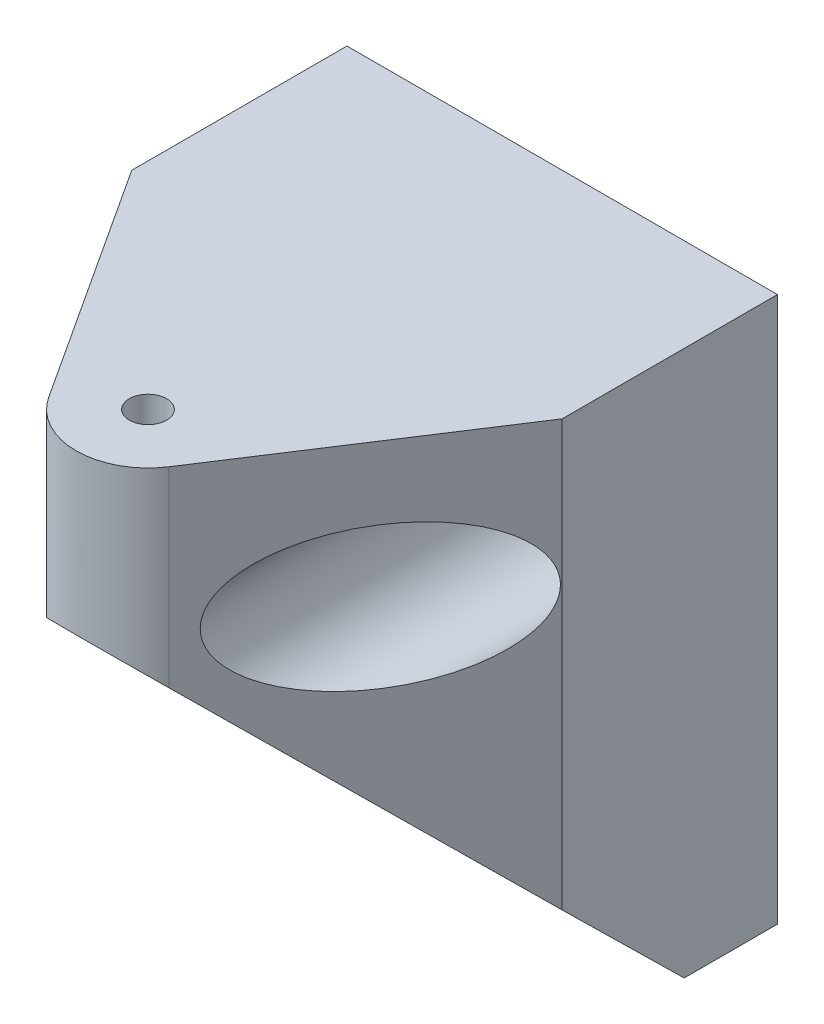
SolidWorks part; units mm, degrees
material "ABS"
ref_plane "Front Plane" through (0, 0, 0) normal (0, 0, 1) x (1, 0, 0)
ref_plane "Top Plane" through (0, 0, 0) normal (0, 1, 0) x (1, 0, 0)
ref_plane "Right Plane" through (0, 0, 0) normal (1, 0, 0) x (0, 0, -1)
sketch "Sketch2" plane through (0, 0, 0) normal (1, 0, 0) x (0, 0, -1)
  line L0 (0, 0) -> (-6.5, 0)
  line L1 (-35, 38) -> (-35, 28)
  line L2 (-35, 38) -> (0, 38)
  line L3 (0, 38) -> (0, 0)
  line L4 (-35, 28) -> (-6.5, 0)
  dimension "D1" = 38
  dimension "D2" = 6.5
  dimension "D3" = 35
  dimension "D4" = 10
extrude "Boss-Extrude1" add sketch "Sketch2" along normal blind 30
sketch "Sketch3" plane through (0, 0, 0) normal (0, 0, -1) x (-1, 0, 0)
  line L0 (-25, 28) -> (-30, 28) construction
  line L1 (-30, 0) -> (-30, 38) construction
  line L2 (-5, 28) -> (0, 28) construction
  line L3 (0, 0) -> (0, 38) construction
  line L4 (-30, 38) -> (0, 38) construction
  circle A0 centre (-25, 28) radius 2.6
  circle A1 centre (-5, 28) radius 2.6
  dimension "D1" = 5.2
  dimension "D3" = 20
  dimension "D4" = 10
extrude "Cut-Extrude1" cut sketch "Sketch3" against normal up to next
sketch "Sketch4" plane through (0, 0, 0) normal (0, 0, -1) x (-1, 0, 0)
  circle A0 centre (-25, 28) radius 4.95
  circle A1 centre (-5, 28) radius 4.95
  dimension "D1" = 9.9
extrude "Cut-Extrude2" cut sketch "Sketch4" against normal up to next from offset 6.5 offset against normal yes
sketch "Sketch5" plane through (0, 38, 0) normal (0, 1, 0) x (1, 0, 0)
  line L0 (30, 0) -> (0, 0) construction
  line L1 (15, -28.87) -> (15, 0) construction
  circle A0 centre (15, -28.87) radius 1.3
  dimension "D1" = 28.87
  dimension "D2" = 2.6
extrude "Cut-Extrude3" cut sketch "Sketch5" against normal up to next
sketch "Sketch6" plane through (0, 38, 0) normal (0, 1, 0) x (1, 0, 0)
  line L0 (0, -35) -> (30, -35)
  line L1 (30, -35) -> (30, -15)
  line L2 (30, 0) -> (30, -35) construction
  line L3 (30, -15) -> (19.1898, -31.5987)
  line L4 (10.8102, -31.5987) -> (0, -15)
  line L5 (0, 0) -> (0, -35) construction
  line L6 (0, -15) -> (0, -35)
  arc A0 (19.1898, -31.5987) -> (10.8102, -31.5987) centre (15, -28.87) cw
  dimension "D2" = 5
  dimension "D1" = 20
extrude "Cut-Extrude4" cut sketch "Sketch6" against normal up to next
